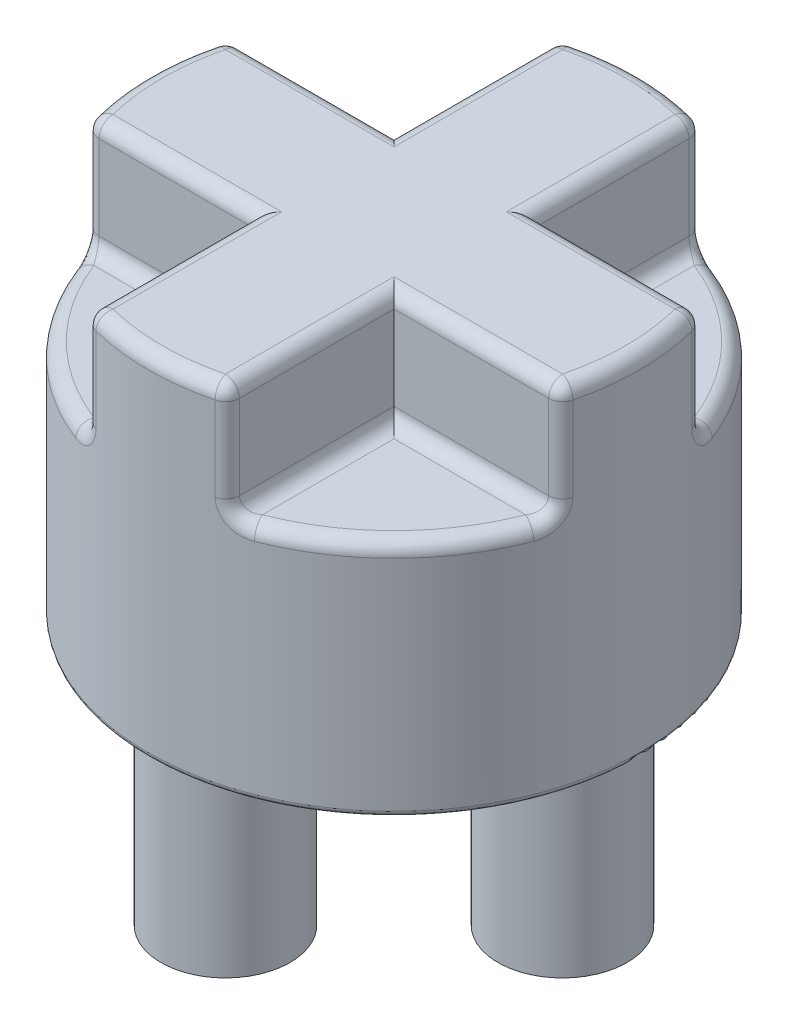
SolidWorks part; units mm, degrees
ref_plane "Front Plane" through (0, 0, 0) normal (0, 0, 1) x (1, 0, 0)
ref_plane "Top Plane" through (0, 0, 0) normal (0, 1, 0) x (1, 0, 0)
ref_plane "Right Plane" through (0, 0, 0) normal (1, 0, 0) x (0, 0, -1)
sketch "Sketch1" plane through (0, 0, 0) normal (0, 1, 0) x (1, 0, 0)
  circle A0 centre (0, 0) radius 11.1125
  dimension "D1" = 22.225
extrude "Boss-Extrude1" add sketch "Sketch1" along normal blind 24.13
sketch "Sketch7" plane through (0, 0, 0) normal (0, -1, 0) x (1, 0, 0)
  circle A0 centre (0, 7.62) radius 1.905
  circle A1 centre (7.62, 0) radius 1.905
  circle A2 centre (0, -7.62) radius 1.905
  circle A3 centre (-7.62, 0) radius 1.905
  point P11 (0, 0)
  dimension "D1" = 3.81
  dimension "D2" = 7.62
  dimension "D3" = 4
extrude "Cut-Extrude8" cut sketch "Sketch7" against normal blind 8.255
sketch "Sketch8" plane through (0, 0, 0) normal (0, -1, 0) x (1, 0, 0)
  circle A24 centre (-7.62, 0) radius 2.921
  circle A25 centre (-7.62, 0) radius 2.921
  circle A27 centre (0, 7.62) radius 2.921
  circle A28 centre (0, 7.62) radius 2.921
  circle A30 centre (7.62, 0) radius 2.921
  circle A31 centre (7.62, 0) radius 2.921
  circle A32 centre (0, 0) radius 13.1338
  circle A33 centre (0, -7.62) radius 2.921
  circle A34 centre (0, -7.62) radius 2.921
  dimension "D1" = 1.016
  dimension "D2" = 1.016
  dimension "D3" = 1.016
  dimension "D4" = 1.016
extrude "Cut-Extrude9" cut sketch "Sketch8" against normal blind 8.255
fillet "Fillet9" radius 0.254 5 edges at (0, 8.255, -11.1125) (-7.62, 8.255, -2.921) (0, 8.255, -10.541) (7.62, 8.255, -2.921) (0, 8.255, 4.699)
sketch "Sketch9" plane through (0, 24.13, 0) normal (0, 1, 0) x (1, 0, 0)
  line L1 (-3.175, 3.175) -> (-12.9287, 3.175)
  line L2 (-3.175, 3.175) -> (-3.175, 12.6111)
  line L3 (-3.175, 12.6111) -> (-12.9287, 12.6111)
  line L4 (-12.9287, 3.175) -> (-12.9287, 12.6111)
  line L5 (3.175, 3.175) -> (11.5695, 3.175)
  line L6 (3.175, 3.175) -> (3.175, 11.7492)
  line L7 (3.175, 11.7492) -> (11.5695, 11.7492)
  line L8 (11.5695, 3.175) -> (11.5695, 11.7492)
  line L9 (3.175, -3.175) -> (12.5192, -3.175)
  line L10 (3.175, -3.175) -> (3.175, -12.8562)
  line L11 (3.175, -12.8562) -> (12.5192, -12.8562)
  line L12 (12.5192, -3.175) -> (12.5192, -12.8562)
  line L13 (-3.175, -3.175) -> (-12.6224, -3.175)
  line L14 (-3.175, -3.175) -> (-3.175, -13.2851)
  line L15 (-3.175, -13.2851) -> (-12.6224, -13.2851)
  line L16 (-12.6224, -3.175) -> (-12.6224, -13.2851)
  dimension "D1" = 6.35
  dimension "D2" = 3.175
  dimension "D3" = 3.175
  dimension "D4" = 3.175
  dimension "D5" = 3.175
  dimension "D6" = 3.175
  dimension "D7" = 3.175
  dimension "D8" = 3.175
extrude "Cut-Extrude10" cut sketch "Sketch9" against normal blind 5.08
fillet "Fillet10" radius 0.635 32 edges at (-3.175, 21.59, 10.6493) (-10.6493, 21.59, 3.175) (3.175, 21.59, 10.6493) (10.6493, 21.59, 3.175) (3.175, 21.59, -10.6493) (10.6493, 21.59, -3.175) (-3.175, 21.59, -10.6493) (-10.6493, 21.59, -3.175) (-7.8577, 19.05, 7.8577) (-6.9121, 19.05, 3.175) (-3.175, 19.05, 6.9121) (3.175, 19.05, 6.9121) (6.9121, 19.05, 3.175) (7.8577, 19.05, 7.8577) (7.8577, 19.05, -7.8577) (6.9121, 19.05, -3.175) (3.175, 19.05, -6.9121) (-3.175, 19.05, -6.9121) (-6.9121, 19.05, -3.175) (-7.8577, 19.05, -7.8577) (-6.9121, 24.13, 3.175) (-11.1125, 24.13, 0) (-6.9121, 24.13, -3.175) (-3.175, 24.13, -6.9121) (0, 24.13, -11.1125) (3.175, 24.13, -6.9121) (6.9121, 24.13, -3.175) (11.1125, 24.13, 0) (6.9121, 24.13, 3.175) (3.175, 24.13, 6.9121) (0, 24.13, 11.1125) (-3.175, 24.13, 6.9121)
